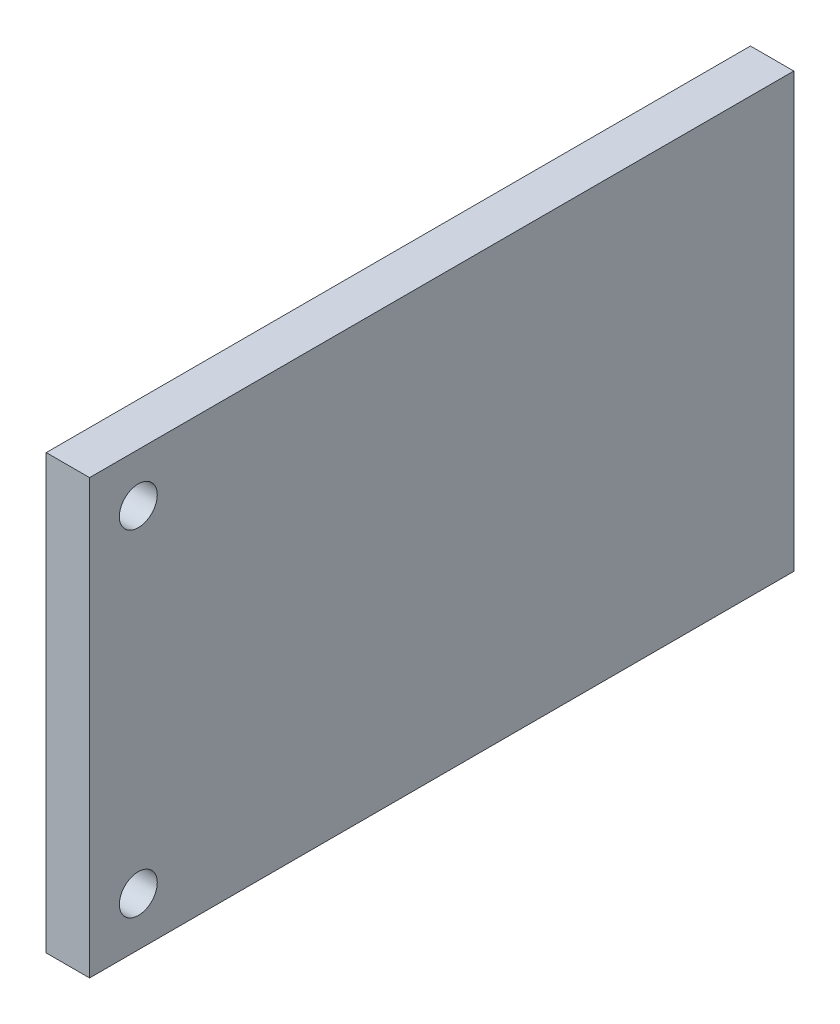
SolidWorks part; units mm, degrees
ref_plane "Płaszczyzna XY" through (0, 0, 0) normal (0, 0, 1) x (1, 0, 0)
ref_plane "Płaszczyzna XZ" through (0, 0, 0) normal (0, 1, 0) x (1, 0, 0)
ref_plane "Płaszczyzna YZ" through (0, 0, 0) normal (1, 0, 0) x (0, 0, -1)
ref_plane "Plane1" through (0, 0, 0) normal (-1, 0, 0) x (0, -1, 0)
sketch "Sketch1" plane through (0, 0, 0) normal (-1, 0, 0) x (0, -1, 0)
  line L0 (-75, -5) -> (5, -5)
  line L1 (5, -5) -> (5, 125)
  line L2 (5, 125) -> (-75, 125)
  line L3 (-75, 125) -> (-75, -5)
  circle A0 centre (-66, 116) radius 3.5
  circle A1 centre (-4, 116) radius 3.5
  dimension "D1" = 7
  dimension "D2" = 5
  dimension "D3" = 4
  dimension "D4" = 66
  dimension "D5" = 75
  dimension "D6" = 116
  dimension "D7" = 125
  dimension "D8" = 5
extrude "Boss-Extrude1" add sketch "Sketch1" against normal blind 8
sketch "Szkic1" plane through (0, 0, 0) normal (-1, 0, 0) x (0, 0, 1)
  line L0 (-3.8732, 3.8732) -> (3.1979, -3.1979)
  line L1 (-3.8732, 3.8732) -> (-0.3377, 7.4087)
  line L2 (3.1979, -3.1979) -> (6.7334, 0.3377)
  line L3 (-0.3377, 7.4087) -> (6.7334, 0.3377)
  line L4 (-5, 75) -> (-5, -5) construction
  line L5 (20.8755, 28.6219) -> (27.9466, 21.5509)
  line L6 (20.8755, 28.6219) -> (24.4111, 32.1575)
  line L7 (27.9466, 21.5509) -> (31.4821, 25.0864)
  line L8 (24.4111, 32.1575) -> (31.4821, 25.0864)
  dimension "D1" = 0
  dimension "D2" = 10
  dimension "D3" = 5
  dimension "D4" = 45
  dimension "D5" = 5
  dimension "D6" = 10
  dimension "D7" = 30
  dimension "D8" = 4.5225
extrude "Dodanie-wyciągnięcie1" add sketch "Szkic1" along normal blind 6
sketch "Szkic2" plane through (0, 0, 0) normal (0, -0.7071, -0.7071) x (1, 0, 0)
  line L0 (-6, -5.4775) -> (0, -5.4775) construction
  line L1 (-4, -3.4775) -> (-2, -3.4775)
  line L2 (-4, -3.4775) -> (-4, 2.5225)
  line L3 (-4, 2.5225) -> (-2, 2.5225)
  line L4 (-2, -3.4775) -> (-2, 2.5225)
  line L5 (-6, 4.5225) -> (0, 4.5225) construction
  line L6 (0, -5.4775) -> (0, 4.5225) construction
  line L7 (-6, -5.4775) -> (-6, 4.5225) construction
  dimension "D1" = 2
  dimension "D2" = 2
  dimension "D3" = 2
  dimension "D4" = 2
extrude "Wytnij-wyciągnięcie1" cut sketch "Szkic2" against normal up to surface (40 mm away) up to face at (-3, 28.6219, 27.9466)
